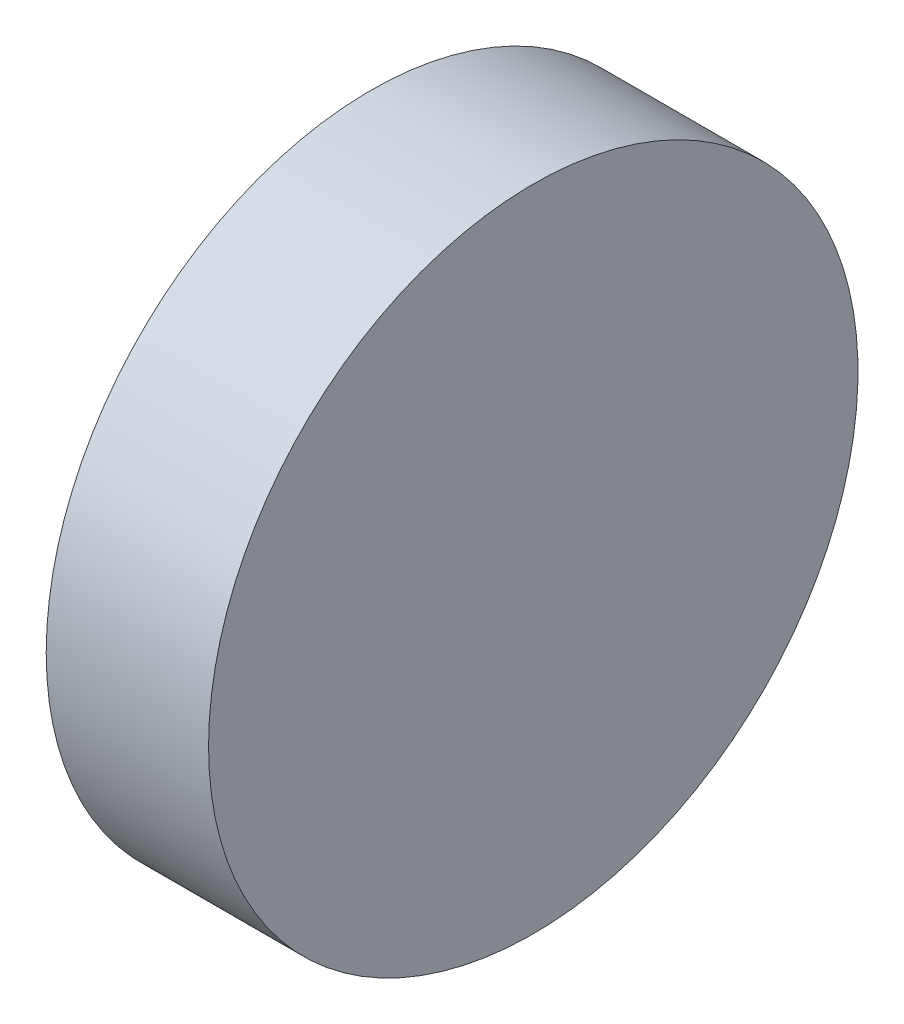
SolidWorks part; units mm, degrees
ref_plane "前视基准面" through (0, 0, 0) normal (0, 0, 1) x (1, 0, 0)
ref_plane "上视基准面" through (0, 0, 0) normal (0, 1, 0) x (1, 0, 0)
ref_plane "右视基准面" through (0, 0, 0) normal (1, 0, 0) x (0, 0, -1)
sketch "草图1" plane through (0, 0, 0) normal (0, 0, 1) x (1, 0, 0)
  line L0 (508.0016, 154.5864) -> (540.062, 154.5864) construction
  line L1 (519.4487, 154.5864) -> (519.4487, 179.9864)
  line L2 (532.1487, 154.5864) -> (532.1487, 179.9864)
  line L3 (519.4487, 179.9864) -> (532.1487, 179.9864)
  line L4 (532.1487, 154.5864) -> (519.4487, 154.5864)
  dimension "D1" = 12.7
revolve "旋转1" add sketch "草图1" angle 360 about L0
